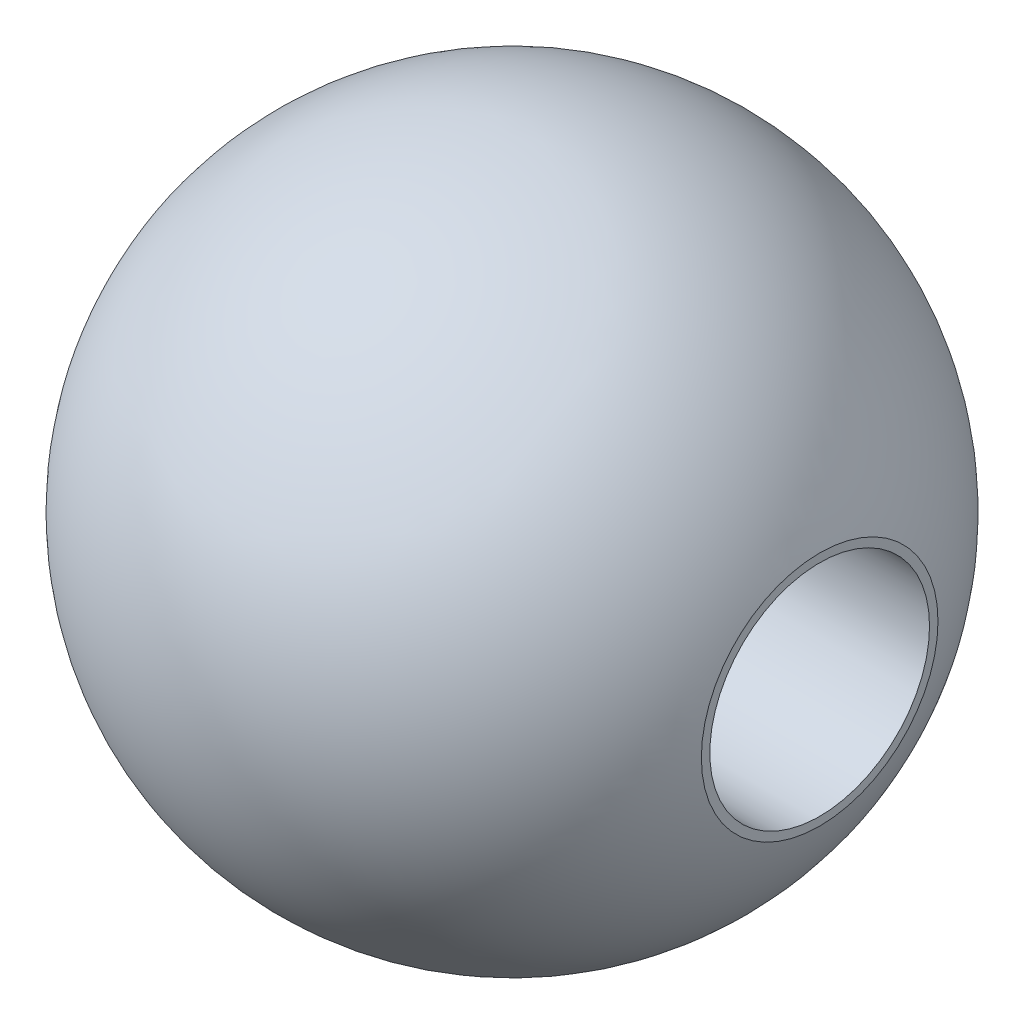
SolidWorks part; units mm, degrees
ref_plane "Front Plane" through (0, 0, 0) normal (0, 0, 1) x (1, 0, 0)
ref_plane "Top Plane" through (0, 0, 0) normal (0, 1, 0) x (1, 0, 0)
ref_plane "Right Plane" through (0, 0, 0) normal (1, 0, 0) x (0, 0, -1)
sketch "Sketch1" plane through (0, 0, 0) normal (0, 1, 0) x (1, 0, 0)
  line L0 (-14, 0) -> (14, 0) construction
  line L1 (-14, 0) -> (-14, 5.3852)
  line L2 (0, 0) -> (0, 19.4953) construction
  line L3 (14, 0) -> (14, 5.3852)
  line L4 (-14, 0) -> (14, 0)
  arc A1 (14, 5.3852) -> (-14, 5.3852) centre (0, 0) ccw
  dimension "D1" = 14
revolve "Revolve1" add sketch "Sketch1" angle 360 about L4
sketch "Sketch2" plane through (14, 0, 0) normal (1, 0, 0) x (0, 0, -1)
  circle A0 centre (0, 0) radius 5
extrude "Cut-Extrude1" cut sketch "Sketch2" against normal through all
